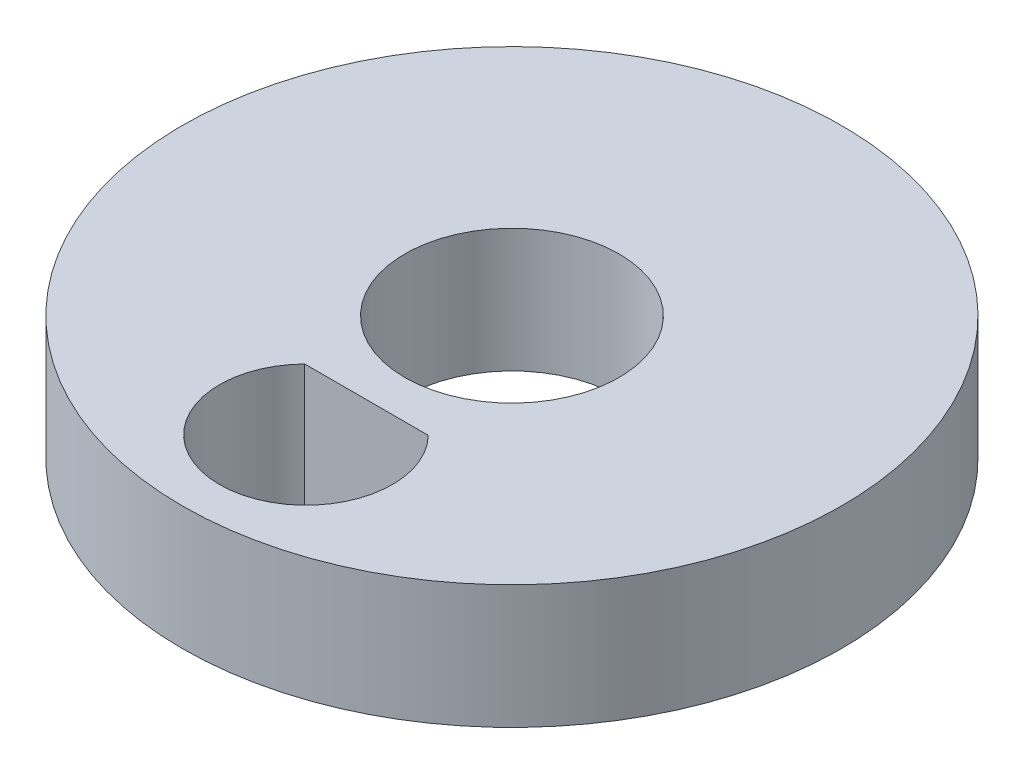
SolidWorks part; units mm, degrees
ref_plane "Front Plane" through (0, 0, 0) normal (0, 0, 1) x (1, 0, 0)
ref_plane "Top Plane" through (0, 0, 0) normal (0, 1, 0) x (1, 0, 0)
ref_plane "Right Plane" through (0, 0, 0) normal (1, 0, 0) x (0, 0, -1)
sketch "Sketch1" plane through (0, 0, 0) normal (0, 1, 0) x (1, 0, 0)
  line L2 (1.5, -3.5303) -> (-1.5, -3.5303)
  circle A0 centre (0, 0) radius 8
  arc A1 (-1.5, -3.5303) -> (1.5, -3.5303) centre (0, -5) ccw
  circle A2 centre (0, 0) radius 2.6
  dimension "D1" = 16
  dimension "D3" = 3
  dimension "D2" = 2.1
  dimension "D5" = 5.2
  dimension "3" = 5
  dimension "D4" = 5
extrude "Boss-Extrude1" add sketch "Sketch1" along normal blind 3
sketch "Sketch2" plane through (0, 3, 0) normal (0, 1, 0) x (1, 0, 0)
  line L2 (1.5, -3.6771) -> (-1.5, -3.6771)
  circle A6 centre (0, 0) radius 8.1
  arc A7 (-1.5, -3.6771) -> (1.5, -3.6771) centre (0, -5) ccw
  circle A8 centre (0, 0) radius 2.5
  point P0 (0, 0)
  dimension "D2" = 3
  dimension "D1" = 2
